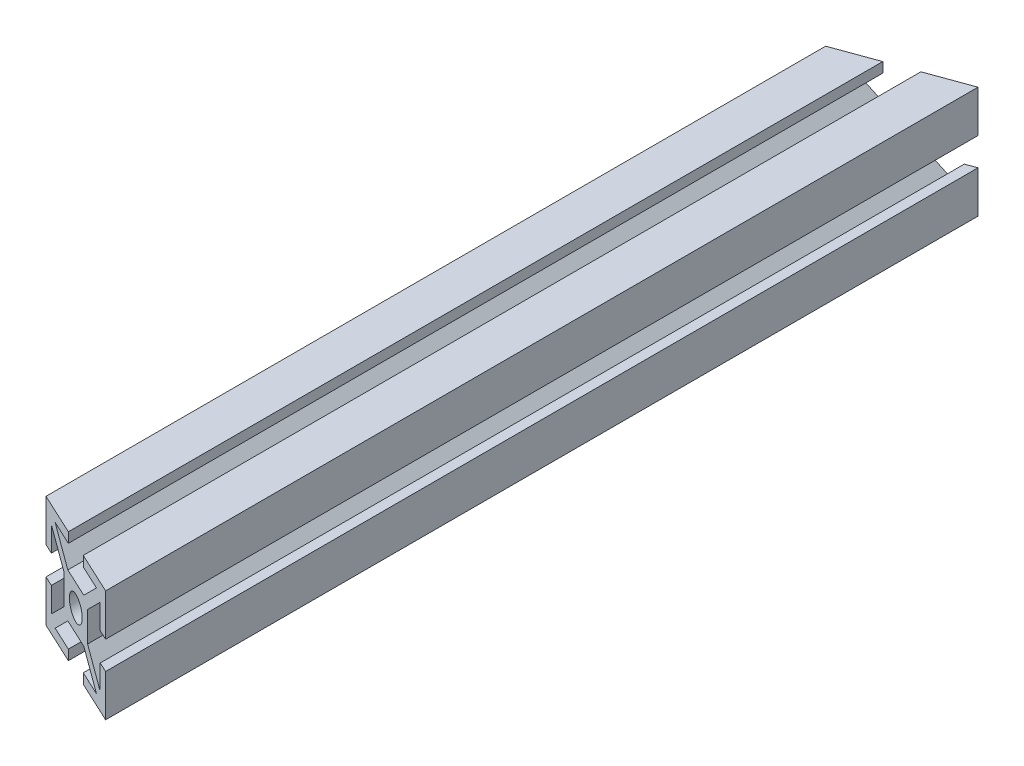
SolidWorks part; units mm, degrees
material "6063-T5"
ref_plane "Front Plane" through (0, 0, 0) normal (0, 0, 1) x (1, 0, 0)
ref_plane "Top Plane" through (0, 0, 0) normal (0, 1, 0) x (1, 0, 0)
ref_plane "Right Plane" through (0, 0, 0) normal (1, 0, 0) x (0, 0, -1)
sketch "Sketch2" plane through (0, 0, 0) normal (0, 0, 1) x (1, 0, 0)
  line L0 (-2.5, 10) -> (-2.5, 8.2)
  line L1 (-10, -10) -> (-2.5, -10)
  line L2 (-10, -10) -> (-10, -2.5)
  line L3 (-10, 10) -> (-2.5, 10)
  line L4 (10, -10) -> (10, -2.5)
  line L5 (-10, -10) -> (10, 10) construction
  line L6 (-10, 10) -> (10, -10) construction
  line L7 (-6.9272, -8.2) -> (-2.5, -8.2)
  line L8 (-8.2, -6.9272) -> (-8.2, -2.5)
  line L9 (-6.9272, 8.2) -> (-2.5, 8.2)
  line L10 (8.2, -6.9272) -> (8.2, -2.5)
  line L13 (2.5, 10) -> (2.5, 8.2)
  line L14 (2.5, 10) -> (10, 10)
  line L15 (2.5, 8.2) -> (6.9272, 8.2)
  line L16 (0, 0) -> (0, 17.5125) construction
  line L17 (-2.15, 2.15) -> (2.15, 2.15) construction
  line L18 (-2.6772, -3.95) -> (2.6772, -3.95)
  line L19 (-3.95, -2.6772) -> (-3.95, 2.6772)
  line L20 (-2.6772, 3.95) -> (2.6772, 3.95)
  line L21 (3.95, -2.6772) -> (3.95, 2.6772)
  line L24 (-2.6772, 3.95) -> (-6.9272, 8.2)
  line L25 (-3.95, 2.6772) -> (-8.2, 6.9272)
  line L26 (10, 2.5) -> (8.2, 2.5)
  line L27 (10, -2.5) -> (8.2, -2.5)
  line L28 (3.95, 2.6772) -> (8.2, 6.9272)
  line L29 (2.6772, 3.95) -> (6.9272, 8.2)
  line L30 (2.5, -10) -> (2.5, -8.2)
  line L31 (-2.5, -10) -> (-2.5, -8.2)
  line L32 (2.6772, -3.95) -> (6.9272, -8.2)
  line L33 (3.95, -2.6772) -> (8.2, -6.9272)
  line L34 (-10, -2.5) -> (-8.2, -2.5)
  line L35 (-10, 2.5) -> (-8.2, 2.5)
  line L36 (-3.95, -2.6772) -> (-8.2, -6.9272)
  line L37 (-2.6772, -3.95) -> (-6.9272, -8.2)
  line L38 (-10, 2.5) -> (-10, 10)
  line L39 (-8.2, 2.5) -> (-8.2, 6.9272)
  line L40 (10, 2.5) -> (10, 10)
  line L41 (8.2, 2.5) -> (8.2, 6.9272)
  line L42 (2.5, -8.2) -> (6.9272, -8.2)
  line L43 (2.5, -10) -> (10, -10)
  circle A0 centre (0, 0) radius 2.15
  point P0 (0, 0)
  point P54 (0, 0)
  dimension "D3" = 4.3
  dimension "D7" = 1.8
  dimension "D1" = 20
  dimension "D4" = 1.8
  dimension "D5" = 5
  dimension "D6" = 1.8
  dimension "D8" = 4
extrude "Boss-Extrude1" add sketch "Sketch2" along normal mid plane 156.2
sketch "Sketch3" plane through (0, 10, 0) normal (0, 1, 0) x (1, 0, 0)
  line L0 (-10, -78.1) -> (10, -78.1)
  line L1 (10, -78.1) -> (-10, -68.7738)
  line L2 (-10, -78.1) -> (-10, 78.1) construction
  line L3 (-10, -68.7738) -> (-10, -78.1)
  dimension "D1" = 25
extrude "Cut-Extrude1" cut sketch "Sketch3" against normal through all
sketch "Sketch4" plane through (0, 10, 0) normal (0, 1, 0) x (1, 0, 0)
  line L0 (10, 78.1) -> (-10, 78.1)
  line L1 (-10, 78.1) -> (-10, 70.8206)
  line L2 (-10, -68.7738) -> (-10, 78.1) construction
  line L3 (-10, 70.8206) -> (10, 78.1)
  dimension "D1" = 20
extrude "Cut-Extrude2" cut sketch "Sketch4" against normal through all
